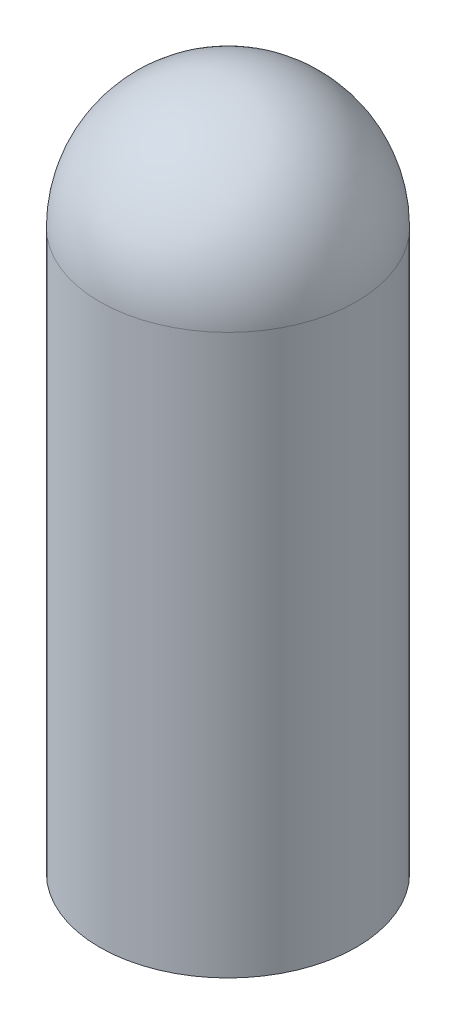
SolidWorks part; units mm, degrees
material "Rubber"
ref_plane "Front Plane" through (0, 0, 0) normal (0, 0, 1) x (1, 0, 0)
ref_plane "Top Plane" through (0, 0, 0) normal (0, 1, 0) x (1, 0, 0)
ref_plane "Right Plane" through (0, 0, 0) normal (1, 0, 0) x (0, 0, -1)
sketch "Sketch1" plane through (0, 0, 0) normal (0, 0, 1) x (1, 0, 0)
  line L0 (-5.9309, 0) -> (-5.9309, 25.8191)
  line L1 (0, 0) -> (0, -6.35) construction
  line L2 (0, -55) -> (0, 55) construction
  line L3 (-5.9309, 0) -> (0, 0)
  line L4 (0, 0) -> (0, 31.75)
  arc A0 (-5.9309, 25.8191) -> (0, 31.75) centre (0, 25.8191) cw
  dimension "D1" = 31.75
  dimension "D2" = 11.8618
  dimension "D3" = 6.35
  dimension "D4" = 25.8191
revolve "Revolve1" add sketch "Sketch1" angle 360 about L1
sketch "Sketch2" plane through (0, 0, 0) normal (0, -1, 0) x (1, 0, 0)
  circle A0 centre (0, 0) radius 5.5499
  circle A1 centre (0, 0) radius 5.9309 construction
  dimension "D1" = 0.381
  dimension "D2" = 11.0998
extrude "Cut-Extrude1" cut sketch "Sketch2" against normal blind 27.7749
